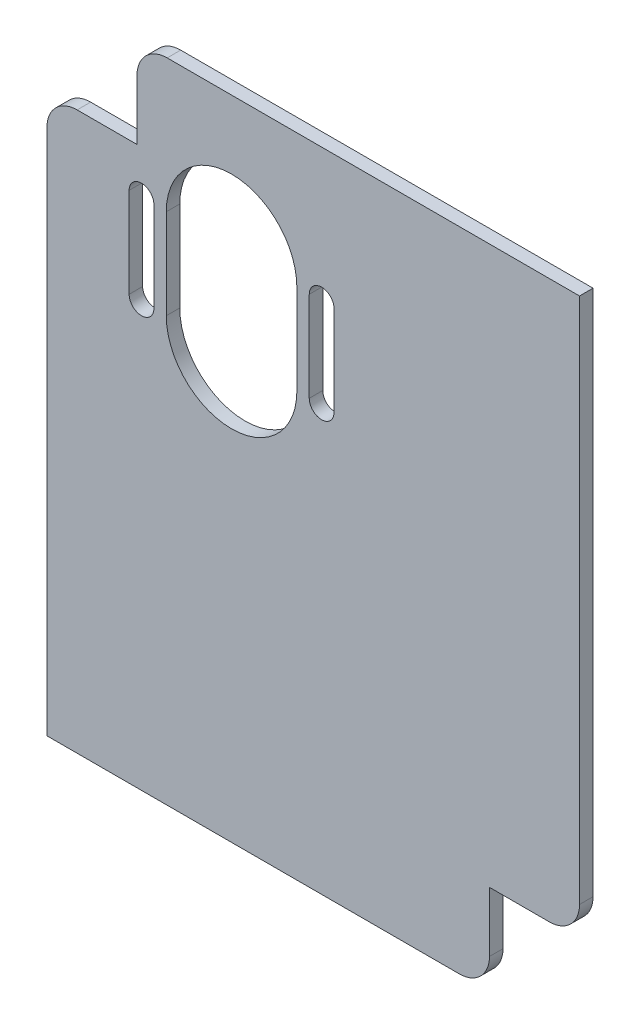
SolidWorks part; units mm, degrees
ref_plane "Front Plane" through (0, 0, 0) normal (0, 0, 1) x (1, 0, 0)
ref_plane "Top Plane" through (0, 0, 0) normal (0, 1, 0) x (1, 0, 0)
ref_plane "Right Plane" through (0, 0, 0) normal (1, 0, 0) x (0, 0, -1)
sketch "Sketch1" plane through (0, 0, 0) normal (0, 0, 1) x (1, 0, 0)
  line L1 (0, 0) -> (118.275, 0)
  line L2 (0, 0) -> (0, 143.74)
  line L3 (0, 143.74) -> (118.275, 143.74)
  line L4 (118.275, 0) -> (118.275, 143.74)
  dimension "D1" = 118.275
  dimension "D2" = 143.74
extrude "Boss-Extrude1" add sketch "Sketch1" along normal blind 3
sketch "Sketch2" plane through (0, 0, 3) normal (0, 0, 1) x (1, 0, 0)
  line L0 (118.275, 143.74) -> (0, 143.74) construction
  line L1 (41, 143.74) -> (41, 0) construction
  line L2 (0, 143.74) -> (0, 0) construction
  line L3 (0, 0) -> (118.275, 0) construction
  line L4 (0, 104.05) -> (118.275, 104.05) construction
  line L5 (118.275, 0) -> (118.275, 143.74) construction
  line L6 (41, 114.05) -> (41, 94.05) construction
  line L7 (55.5, 114.05) -> (55.5, 94.05)
  line L8 (26.5, 114.05) -> (26.5, 94.05)
  line L9 (61, 114.05) -> (61, 94.05) construction
  line L10 (63.75, 114.05) -> (63.75, 94.05)
  line L11 (58.25, 114.05) -> (58.25, 94.05)
  line L12 (21, 114.05) -> (21, 94.05) construction
  line L13 (23.75, 114.05) -> (23.75, 94.05)
  line L14 (18.25, 114.05) -> (18.25, 94.05)
  arc A1 (55.5, 114.05) -> (26.5, 114.05) centre (41, 114.05) ccw
  arc A2 (26.5, 94.05) -> (55.5, 94.05) centre (41, 94.05) ccw
  arc A3 (63.75, 114.05) -> (58.25, 114.05) centre (61, 114.05) ccw
  arc A4 (58.25, 94.05) -> (63.75, 94.05) centre (61, 94.05) ccw
  arc A5 (23.75, 114.05) -> (18.25, 114.05) centre (21, 114.05) ccw
  arc A6 (18.25, 94.05) -> (23.75, 94.05) centre (21, 94.05) ccw
  point P16 (41, 104.05)
  point P21 (61, 104.05)
  point P28 (21, 104.05)
  dimension "D1" = 29
  dimension "D2" = 20
  dimension "D3" = 20
  dimension "D4" = 39.69
  dimension "D5" = 5.5
  dimension "D6" = 5.5
  dimension "D7" = 20
  dimension "D8" = 20
  dimension "D9" = 39.69
  dimension "D10" = 20
  dimension "D11" = 39.69
extrude "Cut-Extrude1" cut sketch "Sketch2" against normal blind 3
sketch "Sketch3" plane through (0, 0, 3) normal (0, 0, 1) x (1, 0, 0)
  line L1 (0, 143.74) -> (20, 143.74)
  line L2 (0, 143.74) -> (0, 123.74)
  line L3 (0, 123.74) -> (20, 123.74)
  line L4 (20, 143.74) -> (20, 123.74)
  line L5 (118.275, 0) -> (98.275, 0)
  line L6 (118.275, 0) -> (118.275, 20)
  line L7 (118.275, 20) -> (98.275, 20)
  line L8 (98.275, 0) -> (98.275, 20)
  dimension "D1" = 20
  dimension "D2" = 20
  dimension "D3" = 20
  dimension "D4" = 20
extrude "Cut-Extrude2" cut sketch "Sketch3" against normal blind 10
fillet "Fillet1" radius 6.7 4 edges at (98.275, 0, 1.5) (118.275, 20, 1.5) (20, 143.74, 1.5) (0, 123.74, 1.5)
